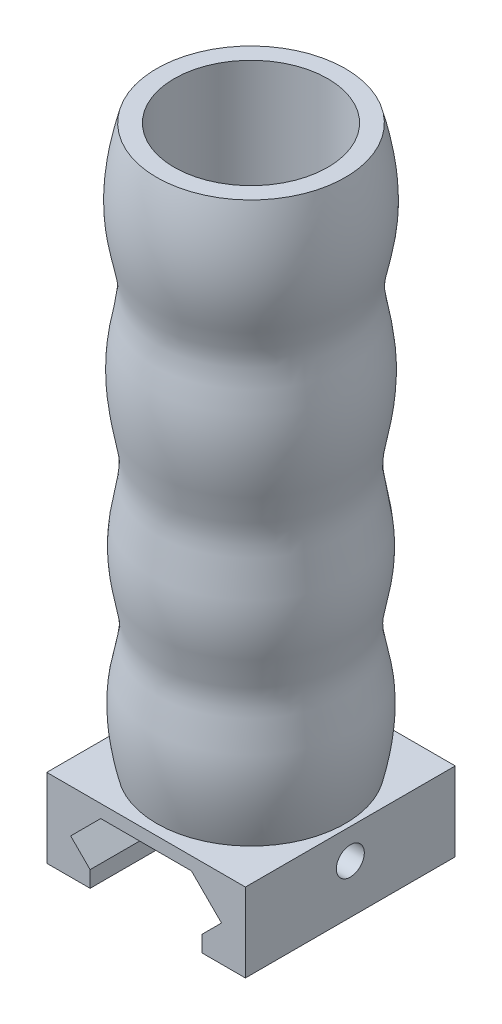
SolidWorks part; units mm, degrees
ref_plane "Front Plane" through (0, 0, 0) normal (0, 0, 1) x (1, 0, 0)
ref_plane "Top Plane" through (0, 0, 0) normal (0, 1, 0) x (1, 0, 0)
ref_plane "Right Plane" through (0, 0, 0) normal (1, 0, 0) x (0, 0, -1)
sketch "Sketch1" plane through (0, 0, 0) normal (0, 0, 1) x (1, 0, 0)
  line L0 (14.2, 13.7619) -> (-14.2, 13.7619)
  line L4 (11.0828, 2.5) -> (8, 2.5)
  line L5 (8, 2.5) -> (8, 4.8172)
  line L6 (8, 4.8172) -> (10.7828, 7.6)
  line L7 (10.7828, 7.6) -> (6.4828, 11.9)
  line L8 (6.4828, 11.9) -> (-6.4828, 11.9)
  line L9 (-6.4828, 11.9) -> (-10.7828, 7.6)
  line L10 (-10.7828, 7.6) -> (-8, 4.8172)
  line L11 (-8, 4.8172) -> (-8, 2.5)
  line L12 (-8, 2.5) -> (-11.0828, 2.5)
  line L19 (-11.0828, 2.5) -> (-14.2, 2.5)
  line L20 (11.0828, 2.5) -> (14.2, 2.5)
  line L21 (14.2, 2.5) -> (14.2, 13.7619)
  line L22 (-14.2, 2.5) -> (-14.2, 13.7619)
  point P0 (0, 11.9)
  point P2 (2.5, 75.5053)
  point P5 (-2.5, 75.5053)
extrude "Boss-Extrude1" add sketch "Sketch1" along normal blind 30
sketch "Sketch3" plane through (14.2, 0, 0) normal (1, 0, 0) x (0, 0, -1)
  line L0 (0, 2.5) -> (0, 13.7619) construction
  circle A0 centre (-15, 9.5) radius 2
  point P0 (0, 7.6)
  dimension "D1" = 15
  dimension "D2" = 7
extrude "Cut-Extrude2" cut sketch "Sketch3" against normal through all contours A0
sketch "Sketch4" plane through (0, 13.7619, 0) normal (0, 1, 0) x (1, 0, 0)
  line L0 (14.2, 0) -> (-14.2, -30)
  line L1 (-14.2, 0) -> (14.2, -30)
  line L2 (-11.0828, 0) -> (-14.2, 0) construction
  line L3 (-14.2, -30) -> (-14.2, 0) construction
  line L4 (14.2, -30) -> (-14.2, -30) construction
  circle A0 centre (0, -15) radius 13.4834
sketch "Sketch9" plane through (0, 0, 0) normal (1, 0, 0) x (0, 0, -1)
  line L0 (-1.5166, 13.7619) -> (-28.4834, 13.7619) construction
  line L1 (0, 13.7619) -> (-30, 13.7619) construction
  line L2 (-28.4834, 93.7619) -> (-15, 93.7619)
  line L3 (-15, 13.7619) -> (-28.4834, 13.7619)
  line L4 (-15, 13.7619) -> (-15, 93.7619)
  spline S0 degree 3 poles (-28.4834, 13.7619) (-31.1451, 24.6923) (-27.1214, 28.7622) (-30.9131, 43.5573) (-27.2956, 49.133) (-31.1948, 65.5653) (-25.7754, 74.2459) (-31.6459, 82.0174) (-28.4834, 93.7619) knots 0 0 0 0 0.086707 0.114659 0.261204 0.315546 0.639761 1 1 1 1
  dimension "D1" = 20
  dimension "D2" = 20
  dimension "D3" = 20
  dimension "D4" = 20
revolve "Revolve2" add sketch "Sketch9" angle 360 about L4
sketch "Sketch11" plane through (0, 93.7619, 0) normal (0, 1, 0) x (1, 0, 0)
  line L0 (14.2, 0) -> (-14.2, -30) construction
  circle A0 centre (0, -15) radius 10.9834
  circle A1 centre (0, -15) radius 13.4834 construction
  dimension "D1" = 2.5
extrude "Cut-Extrude3" cut sketch "Sketch11" against normal up to surface (80 mm away) up to face at (0, 13.7619, 15)
